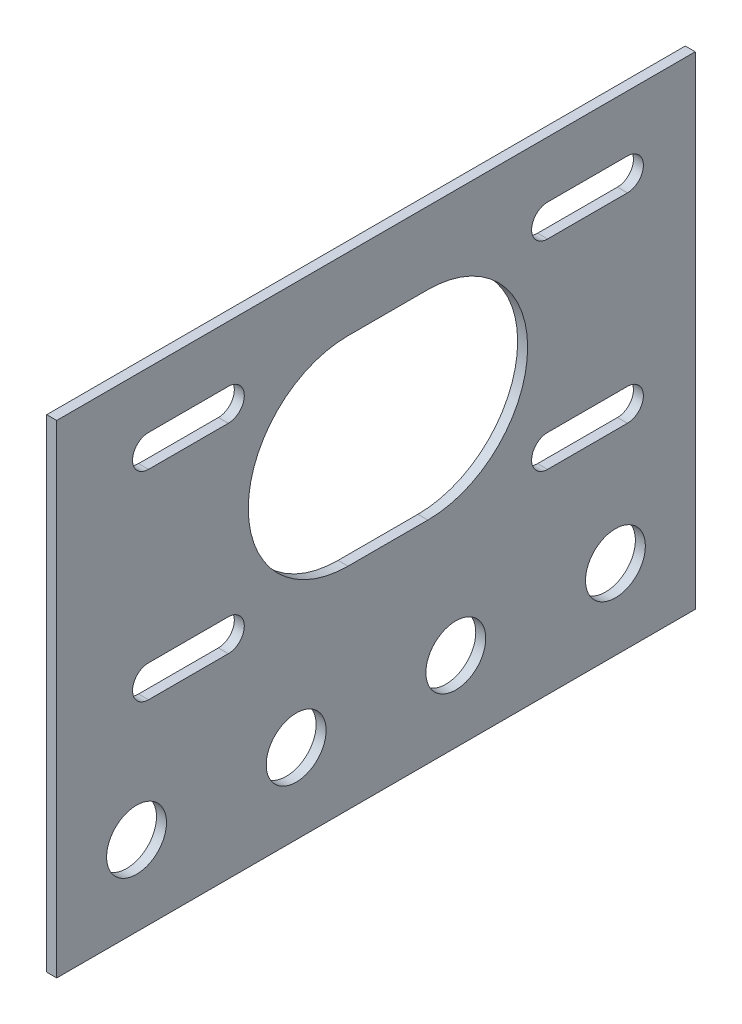
SolidWorks part; units mm, degrees
ref_plane "Front Plane" through (0, 0, 0) normal (0, 0, 1) x (1, 0, 0)
ref_plane "Top Plane" through (0, 0, 0) normal (0, 1, 0) x (1, 0, 0)
ref_plane "Right Plane" through (0, 0, 0) normal (1, 0, 0) x (0, 0, -1)
sketch "Sketch1" plane through (0, 0, 0) normal (1, 0, 0) x (0, 0, -1)
  line L1 (50.8, -38.4175) -> (-50.8, -38.4175)
  line L2 (50.8, -38.4175) -> (50.8, 38.4175)
  line L3 (50.8, 38.4175) -> (-50.8, 38.4175)
  line L4 (-50.8, -38.4175) -> (-50.8, 38.4175)
  line L5 (50.8, -38.4175) -> (-50.8, 38.4175) construction
  line L6 (50.8, 38.4175) -> (-50.8, -38.4175) construction
  point P0 (0, 0)
  dimension "D1" = 101.6
  dimension "D2" = 76.835
extrude "Boss-Extrude1" add sketch "Sketch1" along normal blind 1.5875
sketch "Sketch2" plane through (1.5875, 0, 0) normal (1, 0, 0) x (0, 0, -1)
  line L0 (-50.8, -38.4175) -> (50.8, -38.4175) construction
  line L1 (-50.8, 38.4175) -> (-50.8, -38.4175) construction
  line L2 (-36.195, -4.8387) -> (-23.495, -4.8387) construction
  line L5 (-36.195, -2.2987) -> (-23.495, -2.2987)
  line L8 (-36.195, -7.3787) -> (-23.495, -7.3787)
  line L9 (27.305, -4.8387) -> (40.005, -4.8387) construction
  line L10 (27.305, -2.2987) -> (40.005, -2.2987)
  line L11 (27.305, -7.3787) -> (40.005, -7.3787)
  line L12 (27.305, 26.9113) -> (40.005, 26.9113) construction
  line L13 (27.305, 29.4513) -> (40.005, 29.4513)
  line L14 (27.305, 24.3713) -> (40.005, 24.3713)
  line L15 (-36.195, 26.9113) -> (-23.495, 26.9113) construction
  line L16 (-36.195, 29.4513) -> (-23.495, 29.4513)
  line L17 (-36.195, 24.3713) -> (-23.495, 24.3713)
  line L18 (-29.845, 26.9113) -> (33.655, -4.8387) construction
  line L19 (33.655, 26.9113) -> (-29.845, -4.8387) construction
  line L20 (-4.445, 11.0363) -> (8.255, 11.0363) construction
  line L21 (-4.445, 26.9113) -> (8.255, 26.9113)
  line L22 (-4.445, -4.8387) -> (8.255, -4.8387)
  circle A0 centre (-38.1, -25.7175) radius 4.7625
  circle A1 centre (-12.7, -25.7175) radius 4.7625
  circle A2 centre (12.7, -25.7175) radius 4.7625
  circle A3 centre (38.1, -25.7175) radius 4.7625
  arc A10 (-36.195, -2.2987) -> (-36.195, -7.3787) centre (-36.195, -4.8387) ccw
  arc A11 (-23.495, -7.3787) -> (-23.495, -2.2987) centre (-23.495, -4.8387) ccw
  arc A12 (27.305, -2.2987) -> (27.305, -7.3787) centre (27.305, -4.8387) ccw
  arc A13 (40.005, -7.3787) -> (40.005, -2.2987) centre (40.005, -4.8387) ccw
  arc A14 (27.305, 29.4513) -> (27.305, 24.3713) centre (27.305, 26.9113) ccw
  arc A15 (40.005, 24.3713) -> (40.005, 29.4513) centre (40.005, 26.9113) ccw
  arc A16 (-36.195, 29.4513) -> (-36.195, 24.3713) centre (-36.195, 26.9113) ccw
  arc A17 (-23.495, 24.3713) -> (-23.495, 29.4513) centre (-23.495, 26.9113) ccw
  arc A18 (-4.445, 26.9113) -> (-4.445, -4.8387) centre (-4.445, 11.0363) ccw
  arc A19 (8.255, -4.8387) -> (8.255, 26.9113) centre (8.255, 11.0363) ccw
  point P14 (-29.845, -4.8387)
  point P23 (33.655, -4.8387)
  point P30 (33.655, 26.9113)
  point P37 (-29.845, 26.9113)
  point P46 (1.905, 11.0363)
  dimension "D1" = 9.525
  dimension "D6" = 8.255
  dimension "D5" = 2.54
  dimension "D8" = 15.875
  dimension "D2" = 12.7
  dimension "D3" = 12.7
  dimension "D10" = 12.7
  dimension "D11" = 12.7
  dimension "D12" = 20.8788
  dimension "D4" = 4
  dimension "D9" = 2
  dimension "D7" = 2
extrude "Cut-Extrude1" cut sketch "Sketch2" against normal through all
